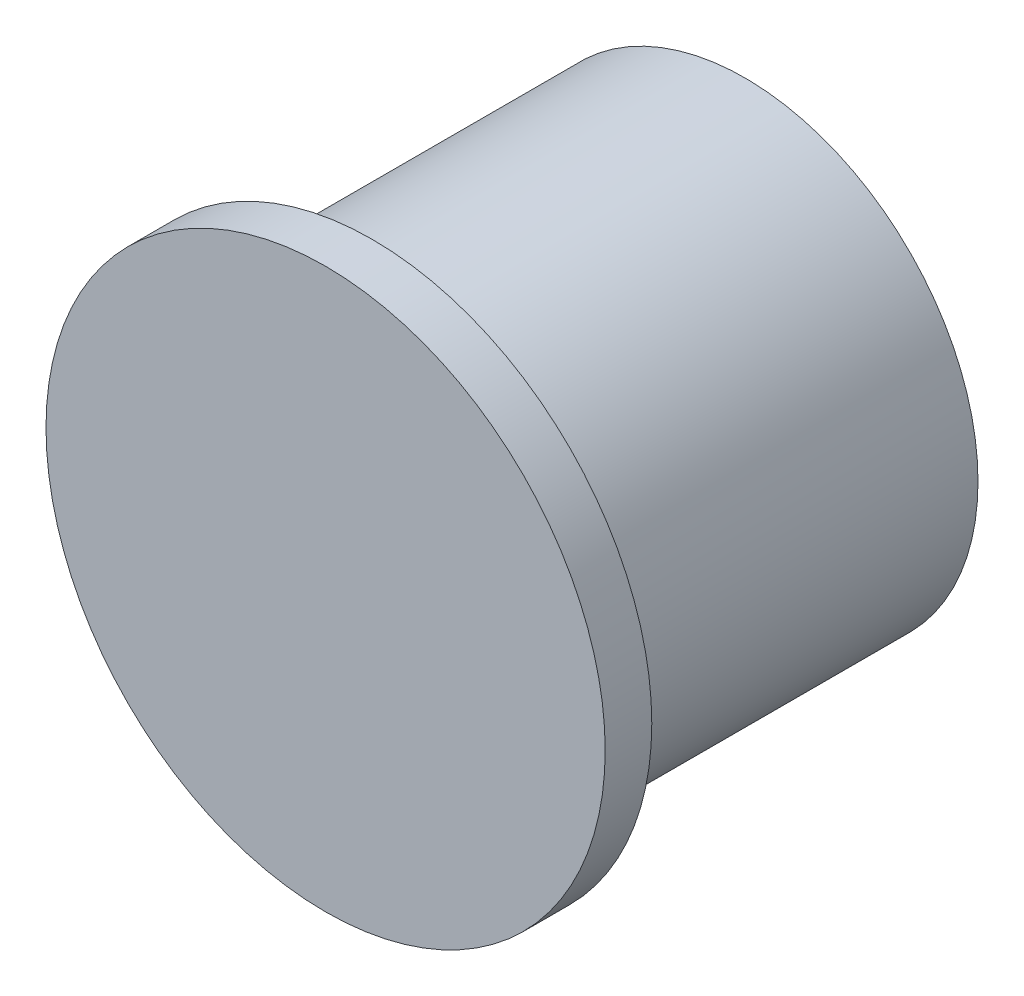
SolidWorks part; units mm, degrees
ref_plane "Front Plane" through (0, 0, 0) normal (0, 0, 1) x (1, 0, 0)
ref_plane "Top Plane" through (0, 0, 0) normal (0, 1, 0) x (1, 0, 0)
ref_plane "Right Plane" through (0, 0, 0) normal (1, 0, 0) x (0, 0, -1)
sketch "Sketch1" plane through (0, 0, 0) normal (0, 0, 1) x (1, 0, 0)
  circle A1 centre (0, 0) radius 5
extrude "Boss-Extrude1" add sketch "Sketch1" along normal blind 8
sketch "Sketch2" plane through (0, 0, 8) normal (0, 0, 1) x (1, 0, 0)
  circle A0 centre (0, 0) radius 6
extrude "Boss-Extrude2" add sketch "Sketch2" along normal blind 1
